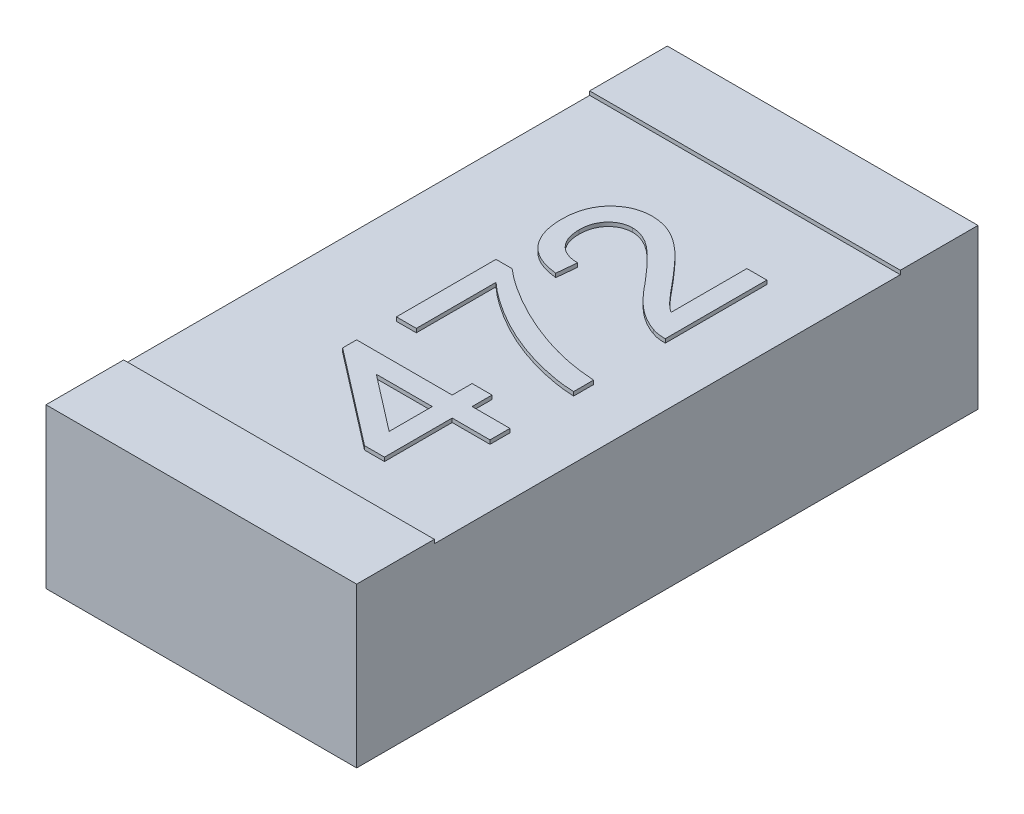
SolidWorks part; units mm, degrees
ref_plane "Спереди" through (0, 0, 0) normal (0, 0, 1) x (1, 0, 0)
ref_plane "Сверху" through (0, 0, 0) normal (0, 1, 0) x (1, 0, 0)
ref_plane "Справа" through (0, 0, 0) normal (1, 0, 0) x (0, 0, -1)
sketch "Эскиз1" plane through (0, 0, 0) normal (0, 1, 0) x (1, 0, 0)
  line L1 (-3.9467, 1.36) -> (-3.1467, 1.36)
  line L2 (-3.9467, 1.36) -> (-3.9467, -0.24)
  line L3 (-3.9467, -0.24) -> (-3.1467, -0.24)
  line L4 (-3.1467, 1.36) -> (-3.1467, -0.24)
  dimension "D1" = 1.6
  dimension "D2" = 0.8
extrude "Бобышка-Вытянуть1" add sketch "Эскиз1" along normal blind 0.4
sketch "Эскиз2" plane through (0, 0.4, 0) normal (0, 1, 0) x (1, 0, 0)
  line L0 (-3.2967, 1.3864) -> (-3.2967, -0.3156) construction
  line L1 (-3.1467, -0.24) -> (-3.1467, 1.36) construction
  line L3 (-3.9467, 1.36) -> (-3.1467, 1.36)
  line L4 (-3.9467, 1.36) -> (-3.9467, 1.16)
  line L5 (-3.9467, 1.16) -> (-3.1467, 1.16)
  line L6 (-3.1467, 1.36) -> (-3.1467, 1.16)
  line L7 (-3.9467, -0.24) -> (-3.1467, -0.24)
  line L8 (-3.9467, -0.24) -> (-3.9467, -0.04)
  line L9 (-3.9467, -0.04) -> (-3.1467, -0.04)
  line L10 (-3.1467, -0.24) -> (-3.1467, -0.04)
  text T0 "472" font "Arial" height 0.4
  dimension "D1" = 0.15
  dimension "D2" = 0.2
  dimension "D3" = 0.2
extrude "Бобышка-Вытянуть2" add sketch "Эскиз2" along normal blind 0.01
